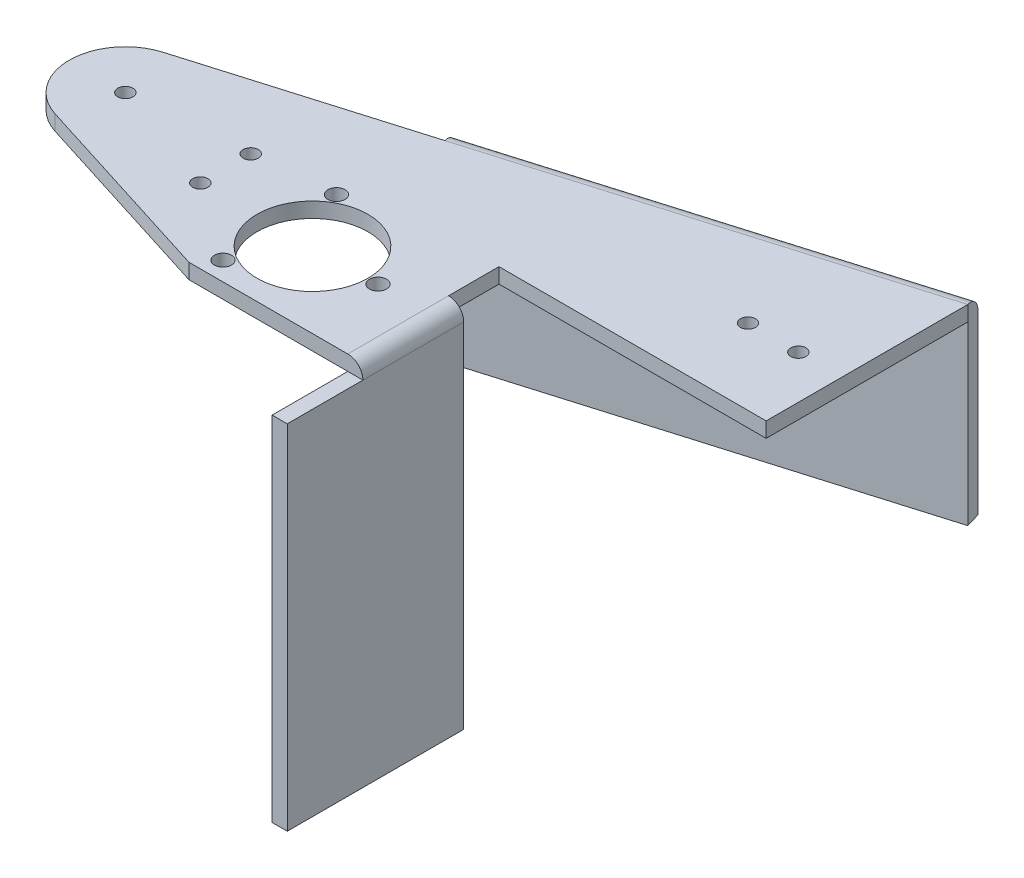
SolidWorks part; units mm, degrees
ref_plane "Plan de face" through (0, 0, 0) normal (0, 0, 1) x (1, 0, 0)
ref_plane "Plan de dessus" through (0, 0, 0) normal (0, 1, 0) x (1, 0, 0)
ref_plane "Plan de droite" through (0, 0, 0) normal (1, 0, 0) x (0, 0, -1)
sketch "Esquisse3" plane through (0, 0, 0) normal (0, -1, 0) x (1, 0, 0)
  line L0 (-464.8441, -40.3599) -> (-411.8441, -40.3599)
  line L1 (-353.8403, -40.3599) -> (-503.8403, -40.3599) construction
  line L2 (-496.3441, -10.3599) -> (-535.1601, -22.5947)
  line L3 (-534.9757, -43.8814) -> (-491.8441, -56.6594)
  line L4 (-491.8441, -56.6594) -> (-492.6963, -59.5358)
  line L5 (-461.8441, -10.3599) -> (-496.3441, -10.3599)
  line L6 (-412.6963, -83.2363) -> (-411.8441, -80.3599)
  line L7 (-411.8441, -40.3599) -> (-411.8441, -80.3599)
  line L8 (-492.6963, -59.5358) -> (-412.6963, -83.2363)
  line L12 (-461.8441, -30.3599) -> (-461.8441, -10.3599)
  line L14 (-464.8441, -30.3599) -> (-461.8441, -30.3599)
  line L16 (-464.8441, -30.3599) -> (-464.8441, -40.3599)
  circle A0 centre (-531.8141, -33.2099) radius 1.5
  circle A1 centre (-508.8441, -35.1135) radius 1.5
  circle A2 centre (-508.8441, -25.1135) radius 1.5
  arc A3 (-535.1601, -22.5947) -> (-534.9757, -43.8814) centre (-531.8141, -33.2099) ccw
  circle A4 centre (-486.8441, -25.3599) radius 11
  circle A5 centre (-473.8441, -25.3599) radius 1.7
  circle A6 centre (-493.3441, -36.6182) radius 1.7
  circle A7 centre (-493.3441, -14.1015) radius 1.7
  circle A8 centre (-420.4555, -55.3599) radius 1.5
  circle A9 centre (-430.4555, -55.3599) radius 1.5
  point P30 (-618.4151, -42.2488)
  dimension "D1" = 3
  dimension "D2" = 3
  dimension "D3" = 3
  dimension "D7" = 3
  dimension "D5" = 13
  dimension "D13" = 10
  dimension "D17" = 11.13
  dimension "D9" = 15
  dimension "D20" = 8.6114
  dimension "D4" = 22
  dimension "D11" = 3.4
  dimension "D25" = 3
  dimension "D32" = 3
  dimension "D6" = 22.97
  dimension "D8" = 20
  dimension "D10" = 22
  dimension "D12" = 3
  dimension "D14" = 15
  dimension "D18" = 3
  dimension "D19" = 22.85
  dimension "D21" = 40
  dimension "D22" = 3
  dimension "D23" = 3
  dimension "D24" = 80
  dimension "D26" = 53
  dimension "D28" = 10
  dimension "D29" = 10
  dimension "D31" = 25
  dimension "D33" = 14.7536
extrude "Boss.-Extru.3" add sketch "Esquisse3" along normal blind 3 separate body
sketch "Esquisse6" plane through (0, -3, 0) normal (0, -1, 0) x (1, 0, 0)
  line L0 (-464.8441, -30.3599) -> (-461.8441, -30.3599)
  line L2 (-464.8441, 4.6401) -> (-464.8441, -30.3599)
  line L3 (-461.8441, -30.3599) -> (-461.8441, -10.3599) construction
  line L4 (-461.8441, 4.6401) -> (-464.8441, 4.6401)
  line L5 (-461.8441, -10.3599) -> (-496.3441, -10.3599) construction
  line L6 (-461.8441, -30.3599) -> (-461.8441, 4.6401)
  dimension "D1" = 35
  dimension "D2" = 3
  dimension "D3" = 15
extrude "Boss.-Extru.4" add sketch "Esquisse6" along normal blind 70
sketch "Esquisse9" plane through (0, -3, 0) normal (0, -1, 0) x (1, 0, 0)
  line L0 (-492.6963, -59.5358) -> (-412.6963, -83.2363)
  line L1 (-492.6963, -59.5358) -> (-491.8441, -56.6594)
  line L2 (-412.6963, -83.2363) -> (-411.8441, -80.3599)
  line L3 (-491.8441, -56.6594) -> (-411.8441, -80.3599)
  dimension "D1" = 3
extrude "Boss.-Extru.5" add sketch "Esquisse9" along normal blind 35
fillet "Congé1" radius 3 2 edges at (-452.6963, 0, -71.3861) (-461.8441, 0, -20.3599)
